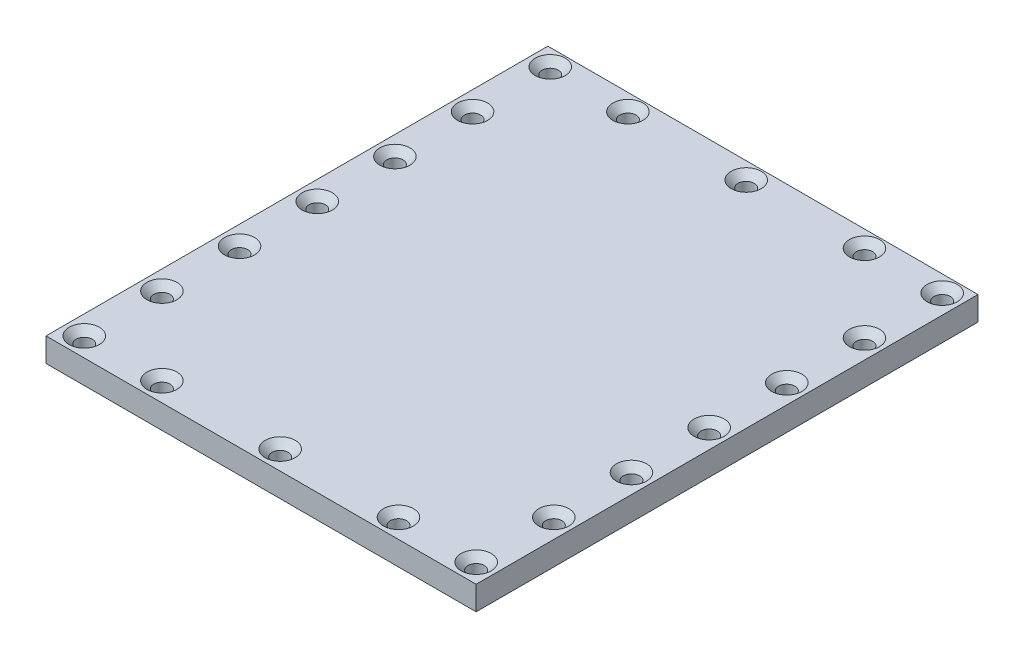
SolidWorks part; units mm, degrees
material "AISI 1020 Steel, Cold Rolled"
ref_plane "Front Plane" through (0, 0, 0) normal (0, 0, 1) x (1, 0, 0)
ref_plane "Top Plane" through (0, 0, 0) normal (0, 1, 0) x (1, 0, 0)
ref_plane "Right Plane" through (0, 0, 0) normal (1, 0, 0) x (0, 0, -1)
sketch "Sketch1" plane through (0, 0, 0) normal (0, 1, 0) x (1, 0, 0)
  line L0 (0, 105) -> (0, 101.5) construction
  line L1 (0, 0) -> (90, 0)
  line L2 (0, 0) -> (0, 105)
  line L3 (0, 105) -> (90, 105)
  line L4 (90, 0) -> (90, 105)
  line L5 (0, 101.5) -> (4, 101.5) construction
  line L6 (0, 0) -> (4, 0) construction
  line L7 (4, 0) -> (4, 4) construction
  line L8 (4, 4) -> (4, 101.5) construction
  line L9 (90, 4) -> (86, 4) construction
  line L10 (86, 4) -> (4, 4) construction
  line L11 (86, 4) -> (86, 101.5) construction
  line L12 (86, 101.5) -> (4, 101.5) construction
  line L13 (45, 105) -> (45, 0) construction
  point P11 (4, 20.25)
  point P13 (4, 36.5)
  point P14 (4, 69)
  point P15 (4, 52.75)
  point P17 (4, 85.25)
  point P19 (86, 20.25)
  point P20 (86, 36.5)
  point P21 (86, 52.75)
  point P22 (86, 69)
  point P23 (86, 85.25)
  point P24 (20.25, 101.5)
  point P25 (69.75, 101.5)
  point P26 (45, 101.5)
  point P27 (20.25, 4)
  point P28 (45, 4)
  point P29 (69.75, 4)
extrude "Extrude1" add sketch "Sketch1" along normal blind 5
sketch "Sketch2" plane through (0, 5, 0) normal (0, 1, 0) x (1, 0, 0)
  line L4 (9, 89.5) -> (9, 16)
  line L5 (16, 7) -> (74, 7)
  line L6 (81, 16) -> (81, 89.5)
  line L7 (16, 96.5) -> (74, 96.5)
  line L8 (83, 7) -> (83, 98)
  line L9 (7, 7) -> (83, 7)
  line L10 (7, 98) -> (7, 7)
  line L11 (83, 98) -> (7, 98)
  line L12 (83, 16) -> (83, 89.5)
  line L13 (16, 9) -> (74, 9)
  line L14 (7, 89.5) -> (7, 16)
  line L15 (16, 98.5) -> (74, 98.5)
  line L16 (81, 96.4868) -> (9, 96.0131) construction
  line L17 (9, 96.0131) -> (9, 8.5132) construction
  line L18 (81, 8.9869) -> (81, 96.4868) construction
  line L19 (9, 8.5132) -> (81, 8.9869) construction
  line L20 (83, 98.5) -> (7, 98) construction
  line L21 (7, 98) -> (7, 6.5) construction
  line L22 (83, 7) -> (83, 98.5) construction
  line L23 (7, 6.5) -> (83, 7) construction
  arc A0 (16, 96.5) -> (9, 89.5) centre (16, 89.5) ccw
  arc A1 (74, 96.5) -> (81, 89.5) centre (74, 89.5) cw
  arc A2 (16, 7) -> (7, 16) centre (16, 16) cw
  arc A3 (83, 16) -> (74, 7) centre (74, 16) cw
  arc A4 (16, 98.5) -> (7, 89.5) centre (16, 89.5) ccw
  arc A5 (74, 98.5) -> (83, 89.5) centre (74, 89.5) cw
  arc A6 (16, 9) -> (9, 16) centre (16, 16) cw
  arc A7 (81, 16) -> (74, 9) centre (74, 16) cw
  dimension "D3" = 7
  dimension "D4" = 9
  dimension "D5" = 9
  dimension "D6" = 7
  dimension "D1" = 7
  dimension "D2" = 2
sketch "Sketch5" plane through (0, 5, 0) normal (0, 1, 0) x (1, 0, 0)
  line L0 (86, 101.5) -> (4, 101.5) construction
  point P0 (4, 101.5)
  point P1 (20.25, 101.5)
  point P3 (45, 101.5)
  point P5 (69.75, 101.5)
  point P8 (86, 101.5)
  point P10 (86, 85.25)
  point P12 (86, 69)
  point P14 (86, 52.75)
  point P16 (86, 36.5)
  point P18 (86, 20.25)
  point P20 (86, 4)
  point P22 (69.75, 4)
  point P24 (45, 4)
  point P26 (20.25, 4)
  point P28 (4, 4)
  point P30 (4, 20.25)
  point P32 (4, 36.5)
  point P34 (4, 52.75)
  point P36 (4, 69)
  point P38 (4, 85.25)
hole_wizard "CSK for M3 Countersunk Flat Head Screw1" positions "3DSketch3" profile "Sketch7" countersink size "M3" standard "ISO" end condition through all
sketch3d "3DSketch3"
  point P0 (4, 5, -4)
  point P3 (4, 5, -20.25)
  point P6 (4, 5, -36.5)
  point P9 (4, 5, -52.75)
  point P12 (4, 5, -69)
  point P15 (4, 5, -85.25)
  point P18 (4, 5, -101.5)
  point P21 (20.25, 5, -101.5)
  point P24 (45, 5, -101.5)
  point P27 (69.75, 5, -101.5)
  point P30 (86, 5, -101.5)
  point P33 (86, 5, -85.25)
  point P36 (86, 5, -69)
  point P39 (86, 5, -52.75)
  point P42 (86, 5, -36.5)
  point P45 (86, 5, -20.25)
  point P48 (86, 5, -4)
  point P51 (69.75, 5, -4)
  point P54 (45, 5, -4)
  point P57 (20.25, 5, -4)
sketch "Sketch7" plane through (4, 5, -4) normal (1, 0, 0) x (0, 0, 1)
  line L0 (0, 0) -> (0, 5)
  line L1 (0, 5) -> (1.7, 5)
  line L2 (1.7, 5) -> (1.7, 1.45)
  line L3 (1.7, 1.45) -> (3.15, 0)
  line L5 (3.15, 0) -> (0, 0)
  line L6 (-1.7, 1.45) -> (-3.15, 0) construction
  line L11 (0, -6.35) -> (0, 107.95) construction
  dimension "Thru Hole Dia." = 3.4
  dimension "Thru Hole Depth" = 5
  dimension "Near C'Sink Dia." = 6.3
  dimension "Near C'Sink Angle" = 90
extrude "Extrude2" cut sketch "Sketch2" along normal blind 0.75 from offset 5
